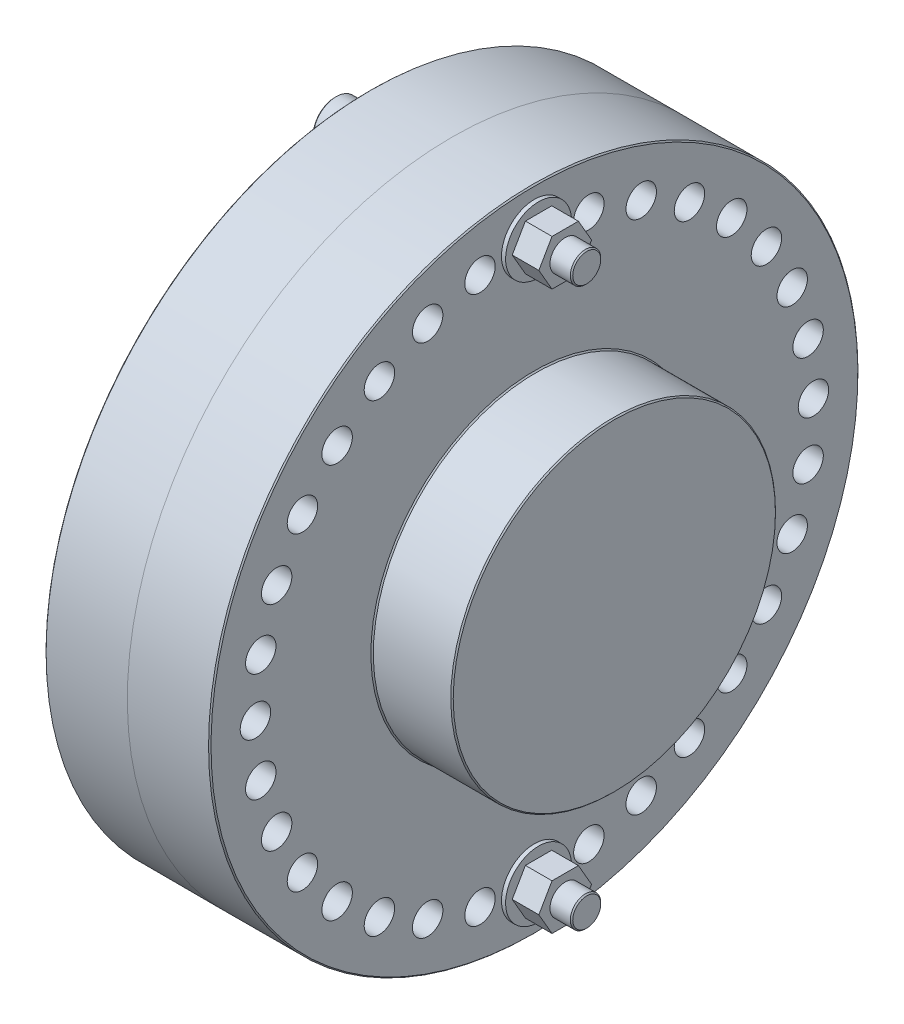
SolidWorks part; units mm, degrees
ref_plane "Front Plane" through (0, 0, 0) normal (0, 0, 1) x (1, 0, 0)
ref_plane "Top Plane" through (0, 0, 0) normal (0, 1, 0) x (1, 0, 0)
ref_plane "Right Plane" through (0, 0, 0) normal (1, 0, 0) x (0, 0, -1)
sketch "Sketch1" plane through (0, 0, 0) normal (0, 0, 1) x (1, 0, 0)
  line L0 (0, 0) -> (-50.8, 0) construction
  line L1 (0, 0) -> (0, 101.6)
  line L2 (0, 101.6) -> (-25.7969, 101.6)
  line L3 (-25.7969, 101.6) -> (-25.7969, 50.8)
  line L4 (-25.7969, 50.8) -> (-50.8, 50.8)
  line L5 (-50.8, 50.8) -> (-50.8, 0)
  line L6 (-50.8, 0) -> (0, 0)
  line L7 (0, 0) -> (-58.9413, 0) construction
  dimension "Dim K" = 50.8
  dimension "Dim A" = 203.2
  dimension "Dim E" = 25.7969
  dimension "Dim C" = 101.6
revolve "Revolve1" add sketch "Sketch1" angle 360 about L7
chamfer "Chamfer2" distance 0.381 angle 45 3 edges at (-50.8, 50.8, 0) (-25.7969, 101.6, 0) (-25.7969, 50.8, 0)
mirror "Mirror1" about plane through (0, 0, 0) normal (1, 0, 0) of bodies 101
sketch "Sketch2" plane through (-25.7969, 0, 0) normal (-1, 0, 0) x (0, 0, 1)
  line L0 (0, 87.3125) -> (0, 0) construction
  circle A0 centre (0, 87.3125) radius 4.7625
  circle A1 centre (0, 0) radius 87.3125 construction
  circle A2 centre (16.0436, 85.8258) radius 4.7625
  circle A3 centre (31.5409, 81.4165) radius 4.7625
  circle A4 centre (45.9641, 74.2346) radius 4.7625
  circle A5 centre (58.8221, 64.5247) radius 4.7625
  circle A6 centre (69.6769, 52.6175) radius 4.7625
  circle A7 centre (78.1589, 38.9185) radius 4.7625
  circle A8 centre (83.9794, 23.8942) radius 4.7625
  circle A9 centre (86.94, 8.0562) radius 4.7625
  circle A10 centre (86.94, -8.0562) radius 4.7625
  circle A11 centre (83.9794, -23.8942) radius 4.7625
  circle A12 centre (78.1589, -38.9185) radius 4.7625
  circle A13 centre (69.6769, -52.6175) radius 4.7625
  circle A14 centre (58.8221, -64.5247) radius 4.7625
  circle A15 centre (45.9641, -74.2346) radius 4.7625
  circle A16 centre (31.5409, -81.4165) radius 4.7625
  circle A17 centre (16.0436, -85.8258) radius 4.7625
  circle A18 centre (0, -87.3125) radius 4.7625
  circle A19 centre (-16.0436, -85.8258) radius 4.7625
  circle A20 centre (-31.5409, -81.4165) radius 4.7625
  circle A21 centre (-45.9641, -74.2346) radius 4.7625
  circle A22 centre (-58.8221, -64.5247) radius 4.7625
  circle A23 centre (-69.6769, -52.6175) radius 4.7625
  circle A24 centre (-78.1589, -38.9185) radius 4.7625
  circle A25 centre (-83.9794, -23.8942) radius 4.7625
  circle A26 centre (-86.94, -8.0562) radius 4.7625
  circle A27 centre (-86.94, 8.0562) radius 4.7625
  circle A28 centre (-83.9794, 23.8942) radius 4.7625
  circle A29 centre (-78.1589, 38.9185) radius 4.7625
  circle A30 centre (-69.6769, 52.6175) radius 4.7625
  circle A31 centre (-58.8221, 64.5247) radius 4.7625
  circle A32 centre (-45.9641, 74.2346) radius 4.7625
  circle A33 centre (-31.5409, 81.4165) radius 4.7625
  circle A34 centre (-16.0436, 85.8258) radius 4.7625
  dimension "D1" = 34
  dimension "Dim H" = 174.625
  dimension "Dim D" = 9.525
extrude "Cut-Extrude1" cut sketch "Sketch2" against normal through all
sketch "Sketch3" plane through (25.7969, 0, 0) normal (1, 0, 0) x (0, 0, -1)
  circle A0 centre (0, 87.3125) radius 4.7625 construction
  circle A1 centre (0, 87.3125) radius 4.7625
  circle A2 centre (17.0338, 85.6348) radius 4.7625
  circle A3 centre (33.413, 80.6662) radius 4.7625
  circle A4 centre (48.5082, 72.5977) radius 4.7625
  circle A5 centre (61.7393, 61.7393) radius 4.7625
  circle A6 centre (72.5977, 48.5082) radius 4.7625
  circle A7 centre (80.6662, 33.413) radius 4.7625
  circle A8 centre (85.6348, 17.0338) radius 4.7625
  circle A9 centre (87.3125, 0) radius 4.7625
  circle A10 centre (85.6348, -17.0338) radius 4.7625
  circle A11 centre (80.6662, -33.413) radius 4.7625
  circle A12 centre (72.5977, -48.5082) radius 4.7625
  circle A13 centre (61.7393, -61.7393) radius 4.7625
  circle A14 centre (48.5082, -72.5977) radius 4.7625
  circle A15 centre (33.413, -80.6662) radius 4.7625
  circle A16 centre (17.0338, -85.6348) radius 4.7625
  circle A17 centre (0, -87.3125) radius 4.7625
  circle A18 centre (-17.0338, -85.6348) radius 4.7625
  circle A19 centre (-33.413, -80.6662) radius 4.7625
  circle A20 centre (-48.5082, -72.5977) radius 4.7625
  circle A21 centre (-61.7393, -61.7393) radius 4.7625
  circle A22 centre (-72.5977, -48.5082) radius 4.7625
  circle A23 centre (-80.6662, -33.413) radius 4.7625
  circle A24 centre (-85.6348, -17.0338) radius 4.7625
  circle A25 centre (-87.3125, 0) radius 4.7625
  circle A26 centre (-85.6348, 17.0338) radius 4.7625
  circle A27 centre (-80.6662, 33.413) radius 4.7625
  circle A28 centre (-72.5977, 48.5082) radius 4.7625
  circle A29 centre (-61.7393, 61.7393) radius 4.7625
  circle A30 centre (-48.5082, 72.5977) radius 4.7625
  circle A31 centre (-33.413, 80.6662) radius 4.7625
  circle A32 centre (-17.0338, 85.6348) radius 4.7625
  circle A33 centre (0, -87.3125) radius 4.7625 construction
  dimension "D1" = 32
extrude "Cut-Extrude2" cut sketch "Sketch3" against normal through all
sketch "Sketch4" plane through (-25.7969, 0, 0) normal (-1, 0, 0) x (0, 0, 1)
  circle A0 centre (0, 87.3125) radius 5.1594
  circle A1 centre (0, 87.3125) radius 10.3188
  dimension "Dim Washer OD" = 20.6375
  dimension "Dim Washer ID" = 10.3187
extrude "Boss-Extrude1" add sketch "Sketch4" along normal blind 1.2954 separate body
mirror "Mirror2" about plane through (0, 0, 0) normal (1, 0, 0) of bodies 106
ref_plane "Plane1" through (42.164, 0, 0) normal (1, 0, 0) x (0, 0, -1)
sketch "Sketch5" plane through (-27.0923, 0, 0) normal (-1, 0, 0) x (0, 0, 1)
  circle A0 centre (0, 87.3125) radius 7.1501
  dimension "Dim head dia" = 14.3002
extrude "Boss-Extrude2" add sketch "Sketch5" along normal blind 9.525 separate body
sketch "Sketch6" plane through (-36.6173, 0, 0) normal (-1, 0, 0) x (0, 0, 1)
  line L1 (0, 82.7298) -> (3.9688, 85.0211)
  line L2 (3.9688, 85.0211) -> (3.9688, 89.6039)
  line L3 (3.9688, 89.6039) -> (0, 91.8952)
  line L4 (0, 91.8952) -> (-3.9687, 89.6039)
  line L5 (-3.9687, 89.6039) -> (-3.9687, 85.0211)
  line L6 (-3.9687, 85.0211) -> (0, 82.7298)
  circle A0 centre (0, 87.3125) radius 3.9687 construction
  dimension "Dim socket hex width" = 7.9375
extrude "Cut-Extrude3" cut sketch "Sketch6" against normal blind 7.9375
sketch "Sketch7" plane through (-27.0923, 0, 0) normal (1, 0, 0) x (0, 0, -1)
  circle A1 centre (0, 87.3125) radius 4.7625 construction
  circle A2 centre (0, 87.3125) radius 4.7625
extrude "Boss-Extrude4" add sketch "Sketch7" along normal up to surface (69.2563 mm away) up to plane "Plane1"
sketch "Sketch8" plane through (27.0923, 0, 0) normal (1, 0, 0) x (0, 0, -1)
  line L1 (4.1244, 94.4562) -> (-4.1244, 94.4562)
  line L2 (-4.1244, 94.4562) -> (-8.2489, 87.3125)
  line L3 (-8.2489, 87.3125) -> (-4.1244, 80.1688)
  line L4 (-4.1244, 80.1688) -> (4.1244, 80.1687)
  line L5 (4.1244, 80.1687) -> (8.2489, 87.3125)
  line L6 (8.2489, 87.3125) -> (4.1244, 94.4562)
  circle A0 centre (0, 87.3125) radius 4.7625
  circle A1 centre (0, 87.3125) radius 4.7625 construction
  circle A2 centre (0, 87.3125) radius 7.1437 construction
  dimension "Dim nut width" = 14.2875
extrude "Boss-Extrude5" add sketch "Sketch8" along normal blind 8.3344 separate body
chamfer "Chamfer1" distance 0.381 angle 45 2 edges at (42.164, 92.075, 0) (-36.6173, 80.1624, 0)
mirror "Mirror3" about plane through (0, 0, 0) normal (0, 1, 0) of bodies 112 111 107 106
